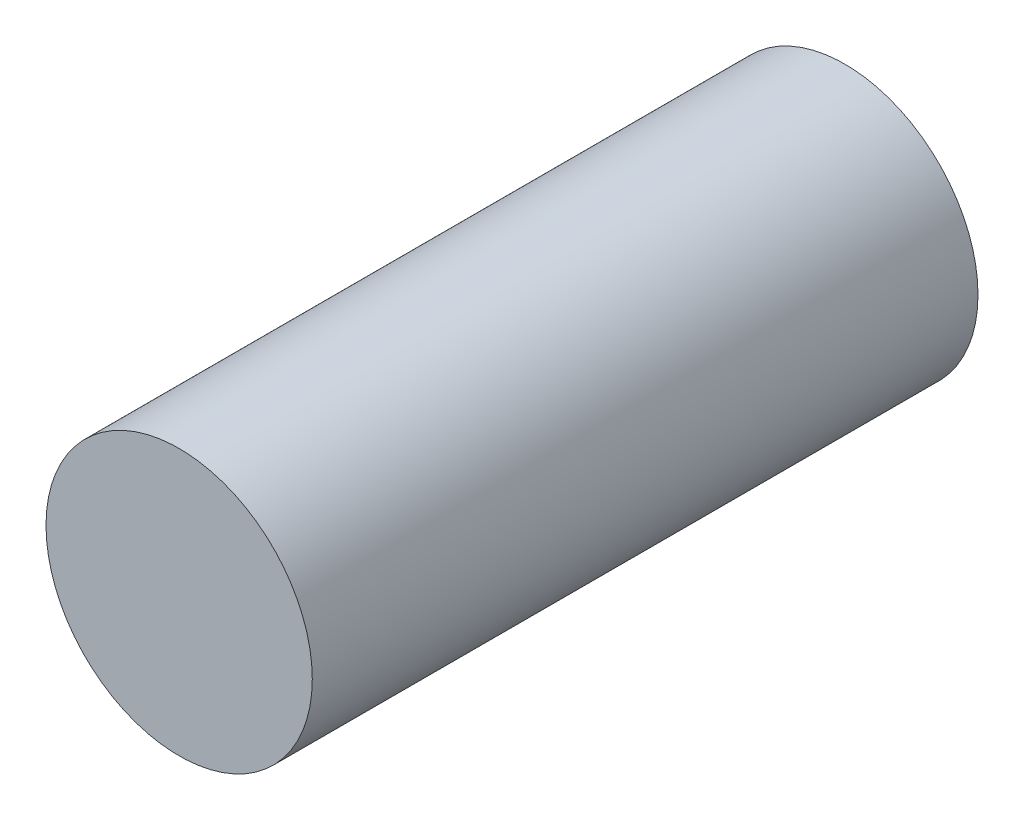
SolidWorks part; units mm, degrees
ref_plane "Alzado" through (0, 0, 0) normal (0, 0, 1) x (1, 0, 0)
ref_plane "Planta" through (0, 0, 0) normal (0, 1, 0) x (1, 0, 0)
ref_plane "Vista lateral" through (0, 0, 0) normal (1, 0, 0) x (0, 0, -1)
sketch "Croquis1" plane through (0, 0, 0) normal (0, 0, 1) x (1, 0, 0)
  circle A0 centre (0, 0) radius 6.35
  dimension "D1" = 12.7
extrude "Saliente-Extruir1" add sketch "Croquis1" along normal blind 31.75
